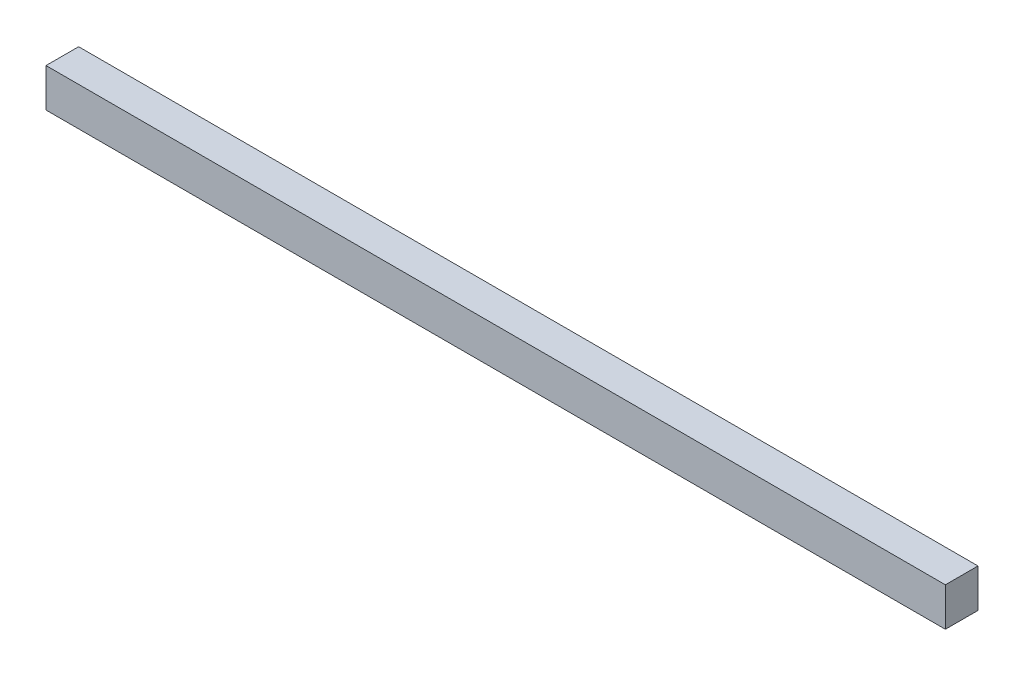
SolidWorks part; units mm, degrees
ref_plane "Front Plane" through (0, 0, 0) normal (0, 0, 1) x (1, 0, 0)
ref_plane "Top Plane" through (0, 0, 0) normal (0, 1, 0) x (1, 0, 0)
ref_plane "Right Plane" through (0, 0, 0) normal (1, 0, 0) x (0, 0, -1)
sketch "Sketch1" plane through (0, 0, 0) normal (0, 0, 1) x (1, 0, 0)
  line L1 (0, 0) -> (70, 0)
  line L2 (0, 0) -> (0, -3)
  line L3 (0, -3) -> (70, -3)
  line L4 (70, 0) -> (70, -3)
  dimension "D1" = 70
  dimension "D2" = 3
extrude "Extrude1" add sketch "Sketch1" along normal blind 2.54
